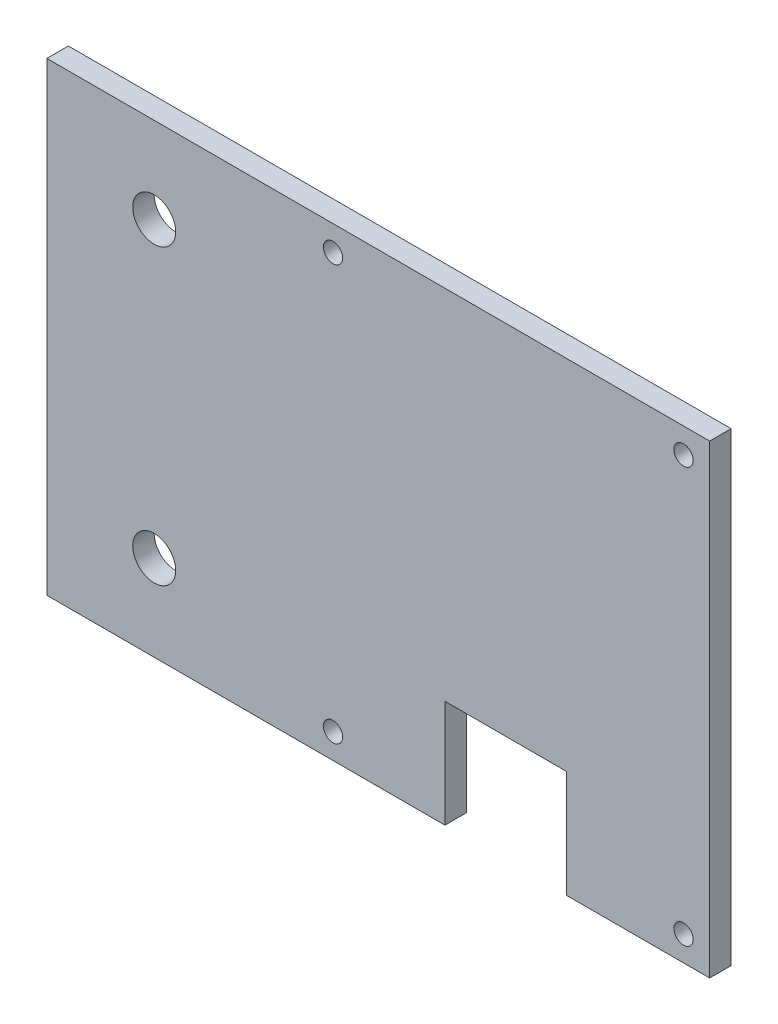
SolidWorks part; units mm, degrees
ref_plane "Front Plane" through (0, 0, 0) normal (0, 0, 1) x (1, 0, 0)
ref_plane "Top Plane" through (0, 0, 0) normal (0, 1, 0) x (1, 0, 0)
ref_plane "Right Plane" through (0, 0, 0) normal (1, 0, 0) x (0, 0, -1)
sketch "Sketch1" plane through (0, 0, 0) normal (0, 0, 1) x (1, 0, 0)
  line L1 (0, 0) -> (92.65, 0)
  line L2 (0, 0) -> (0, 65)
  line L3 (0, 65) -> (92.65, 65)
  line L4 (92.65, 0) -> (92.65, 65)
  circle A0 centre (15, 53) radius 3
  circle A1 centre (40, 61.5) radius 1.35
  circle A2 centre (40, 3.5) radius 1.35
  dimension "D3" = 6
  dimension "D4" = 15
  dimension "D5" = 12
  dimension "D6" = 58
  dimension "D7" = 2.7
  dimension "D8" = 2.7
  dimension "D9" = 3.5
  dimension "D10" = 52.65
  dimension "D11" = 52.65
  dimension "D1" = 65
  dimension "D2" = 92.65
extrude "Boss-Extrude1" add sketch "Sketch1" along normal blind 3
sketch "Sketch2" plane through (0, 0, 3) normal (0, 0, 1) x (1, 0, 0)
  line L1 (0, 0) -> (92.65, 0) construction
  circle A0 centre (89, 61.5) radius 1.35
  circle A1 centre (89, 3.5) radius 1.35
  circle A2 centre (40, 3.5) radius 1.35 construction
  circle A3 centre (40, 61.5) radius 1.35 construction
  dimension "D1" = 2.7
  dimension "D2" = 2.7
  dimension "D3" = 58
  dimension "D4" = 49
  dimension "D5" = 49
  dimension "D6" = 3.5
extrude "Cut-Extrude1" cut sketch "Sketch2" against normal through all
sketch "Sketch3" plane through (0, 0, 3) normal (0, 0, 1) x (1, 0, 0)
  line L0 (0, 0) -> (92.65, 0) construction
  line L1 (55.65, 0) -> (72.65, 0)
  line L2 (55.65, 0) -> (55.65, 15)
  line L3 (55.65, 15) -> (72.65, 15)
  line L4 (72.65, 0) -> (72.65, 15)
  line L5 (92.65, 0) -> (92.65, 65) construction
  dimension "D1" = 17
  dimension "D2" = 15
  dimension "D3" = 20
extrude "Cut-Extrude2" cut sketch "Sketch3" against normal through all
sketch "Sketch4" plane through (0, 0, 0) normal (0, 0, -1) x (-1, 0, 0)
  line L0 (0, 0) -> (-55.65, 0) construction
  line L1 (0, 65) -> (0, 0) construction
  circle A0 centre (-15, 12) radius 3
  dimension "D1" = 6
  dimension "D2" = 12
  dimension "D3" = 15
extrude "Cut-Extrude3" cut sketch "Sketch4" against normal through all
